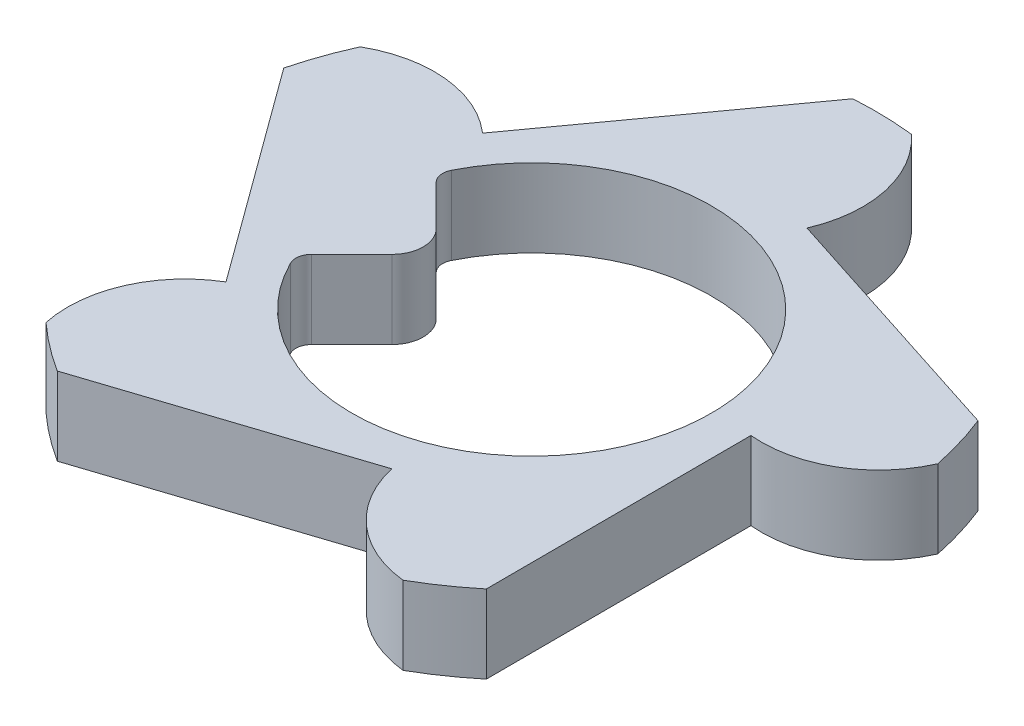
SolidWorks part; units mm, degrees
ref_plane "Front Plane" through (0, 0, 0) normal (0, 0, 1) x (1, 0, 0)
ref_plane "Top Plane" through (0, 0, 0) normal (0, 1, 0) x (1, 0, 0)
ref_plane "Right Plane" through (0, 0, 0) normal (1, 0, 0) x (0, 0, -1)
sketch "Sketch1" plane through (0, 0, 0) normal (0, 1, 0) x (1, 0, 0)
  line L0 (0, 0) -> (-1.65, 0) construction
  line L1 (0, 0) -> (-1.6298, 0.2571) construction
  line L2 (0, 0) -> (-1.3349, -0.9698) construction
  line L3 (0, 0) -> (1.65, 0) construction
  line L4 (0, 0) -> (0.4326, -1.3315) construction
  line L5 (-1.1307, -0.8255) -> (-2.1314, 0.5451)
  line L6 (0, 0) -> (0, -1.4) construction
  line L7 (0, 0) -> (-1.3349, 0.9698) construction
  line L8 (0, 0) -> (0.5099, 1.5692) construction
  line L9 (0, 0) -> (1.65, 0) construction
  line L10 (0, 0) -> (0.5099, -1.5692) construction
  line L11 (-1.1345, 0.8203) -> (-0.1402, 2.1955)
  line L12 (0.4295, 1.3325) -> (2.0447, 0.8118)
  line L13 (1.4, 0.0032) -> (1.4039, -1.6938)
  line L14 (0.4357, -1.3305) -> (-1.1771, -1.8586)
  arc A0 (-2.0044, 0.9069) -> (-2.1314, 0.5451) centre (0, 0) ccw
  circle A1 centre (0, 0) radius 1.65 construction
  circle A2 centre (0, 0) radius 1.4 construction
  arc A3 (0.2431, 2.1865) -> (-0.1402, 2.1955) centre (0, 0) ccw
  arc A4 (-1.1345, 0.8203) -> (-2.0044, 0.9069) centre (-1.6298, 0.2571) ccw
  arc A5 (0.4295, 1.3325) -> (0.2431, 2.1865) centre (-0.2591, 1.6295) ccw
  arc A6 (2.1546, 0.4445) -> (2.0447, 0.8118) centre (0, 0) ccw
  arc A7 (1.4, 0.0032) -> (2.1546, 0.4445) centre (1.4697, 0.75) ccw
  arc A8 (1.0885, -1.9118) -> (1.4039, -1.6938) centre (0, 0) ccw
  arc A9 (0.4357, -1.3305) -> (1.0885, -1.9118) centre (1.1675, -1.166) ccw
  arc A10 (-1.4819, -1.626) -> (-1.1771, -1.8586) centre (0, 0) ccw
  arc A11 (-1.1307, -0.8255) -> (-1.4819, -1.626) centre (-0.7482, -1.4706) ccw
  point P20 (0, 0)
  point P36 (0, 0)
  point P38 (0, 0)
  point P46 (0, 0)
  dimension "D1" = 4.4
  dimension "D2" = 3.3
  dimension "D3" = 2.8
  dimension "D5" = 0.75
  dimension "D4" = 72
  dimension "D6" = 72
  dimension "D7" = 5
extrude "Boss-Extrude1" add sketch "Sketch1" along normal blind 0.5
sketch "Sketch2" plane through (0, 0.5, 0) normal (0, 1, 0) x (1, 0, 0)
  line L0 (0, 0) -> (-1.15, 0) construction
  line L1 (-1.0591, 0.4481) -> (-0.611, 0)
  line L2 (-0.611, 0) -> (-1.0591, -0.4481)
  arc A0 (-1.0591, -0.4481) -> (-1.0591, 0.4481) centre (0, 0) ccw
  dimension "D1" = 2.3
  dimension "D2" = 0.611
extrude "Cut-Extrude1" cut sketch "Sketch2" against normal up to next
fillet "Fillet1" radius 0.1 2 edges at (-1.0591, 0.25, 0.4481) (-1.0591, 0.25, -0.4481)
fillet "Fillet2" radius 0.2 1 edges at (-0.611, 0.25, 0)
